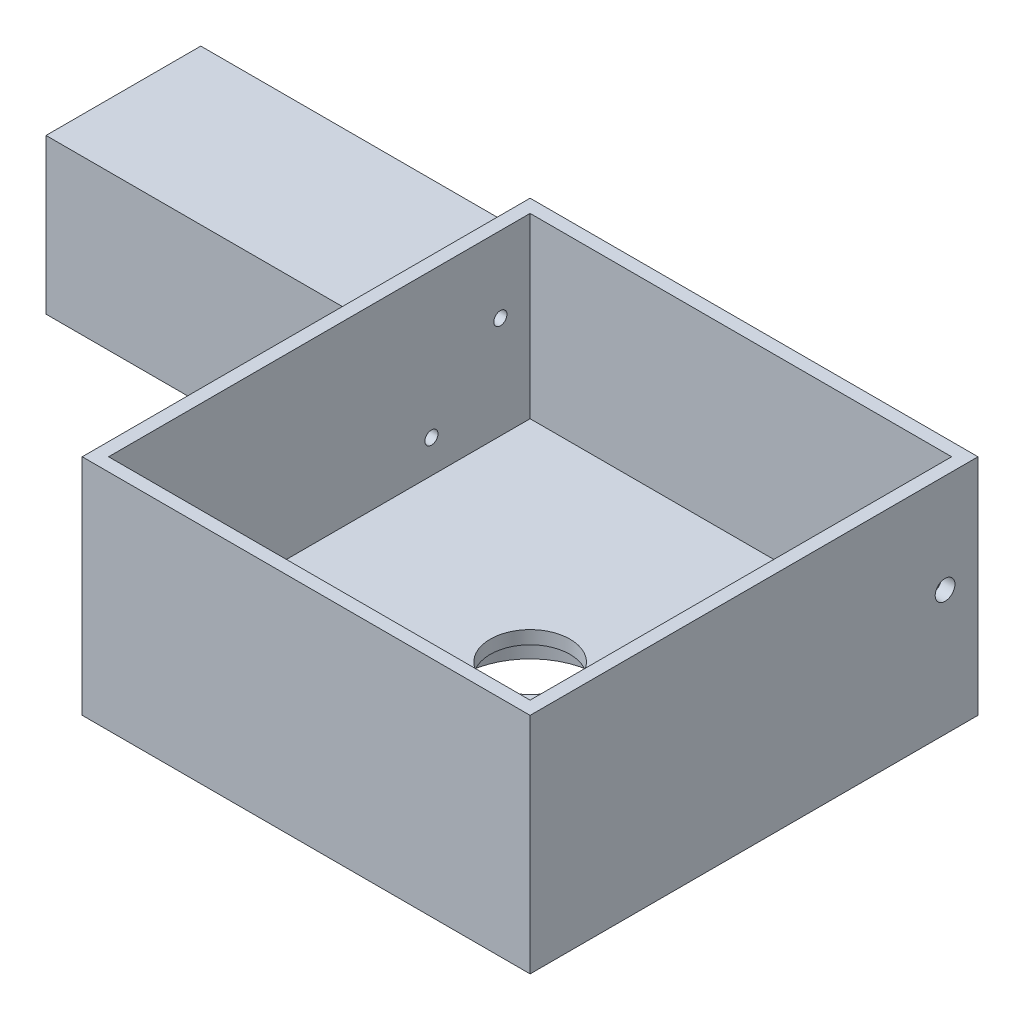
SolidWorks part; units mm, degrees
ref_plane "Front Plane" through (0, 0, 0) normal (0, 0, 1) x (1, 0, 0)
ref_plane "Top Plane" through (0, 0, 0) normal (0, 1, 0) x (1, 0, 0)
ref_plane "Right Plane" through (0, 0, 0) normal (1, 0, 0) x (0, 0, -1)
sketch "Sketch1" plane through (0, 0, 0) normal (0, 1, 0) x (1, 0, 0)
  line L1 (-34, -34) -> (34, -34)
  line L2 (-34, -34) -> (-34, 34)
  line L3 (-34, 34) -> (34, 34)
  line L4 (34, -34) -> (34, 34)
  line L5 (-34, -34) -> (34, 34) construction
  line L6 (-34, 34) -> (34, -34) construction
  point P0 (0, 0)
  dimension "D1" = 68
extrude "Boss-Extrude1" add sketch "Sketch1" along normal blind 34
sketch "Sketch2" plane through (0, 0, 0) normal (0, 1, 0) x (1, 0, 0)
  line L1 (-32, -32) -> (32, -32)
  line L2 (-32, -32) -> (-32, 32)
  line L3 (-32, 32) -> (32, 32)
  line L4 (32, -32) -> (32, 32)
  line L5 (-32, -32) -> (32, 32) construction
  line L6 (-32, 32) -> (32, -32) construction
  point P0 (0, 0)
  dimension "D1" = 64
extrude "Cut-Extrude1" cut sketch "Sketch2" against normal blind 27 from surface at 34 starting at face at (0, 34, 0)
sketch "Sketch5" plane through (0, 0, 0) normal (0, 1, 0) x (1, 0, 0)
  circle A0 centre (0, 0) radius 6.05
  dimension "D1" = 12.1
sketch "Sketch6" plane through (0, 0, 0) normal (0, -1, 0) x (1, 0, 0)
  circle A0 centre (0, 0) radius 10.5
  dimension "D1" = 21
extrude "Cut-Extrude10" cut sketch "Sketch6" against normal blind 5 from surface at 0 starting at face at (0, 0, 0)
sketch "Sketch7" plane through (0, 0, 0) normal (0, -1, 0) x (-1, 0, 0)
  line L0 (-34, 34) -> (34, -34) construction
  line L1 (-34, -34) -> (34, 34) construction
  line L3 (-15, 15) -> (15, 15)
  line L4 (-15, 15) -> (-15, -15)
  line L5 (-15, -15) -> (15, -15)
  line L6 (15, 15) -> (15, -15)
  line L7 (-13, 13) -> (13, 13)
  line L8 (-13, 13) -> (-13, -13)
  line L9 (-13, -13) -> (13, -13)
  line L10 (13, 13) -> (13, -13)
  point P8 (0, 0)
  dimension "D1" = 30
  dimension "D2" = 26
extrude "Cut-Extrude11" cut sketch "Sketch7" against normal blind 2
sketch "Sketch8" plane through (32, 0, 0) normal (-1, 0, 0) x (0, 0, 1)
  line L0 (32, 7) -> (-32, 7) construction
  line L1 (-32, 7) -> (-32, 34) construction
  circle A0 centre (-29, 19) radius 1.5
  dimension "D1" = 3
  dimension "D2" = 12
  dimension "D3" = 3
extrude "Cut-Extrude12" cut sketch "Sketch8" against normal through all
sketch "Sketch9" plane through (-34, 0, 0) normal (-1, 0, 0) x (0, 0, 1)
  line L0 (-34, 29) -> (-10.5, 5.5) construction
  line L1 (-34, 5.5) -> (-10.5, 5.5)
  line L2 (-34, 5.5) -> (-34, 29)
  line L3 (-34, 29) -> (-10.5, 29)
  line L4 (-10.5, 5.5) -> (-10.5, 29)
  line L5 (-10.5, 29) -> (-34, 5.5) construction
  line L6 (-34, 34) -> (-34, 0) construction
  line L7 (-34, 0) -> (34, 0) construction
  circle A0 centre (-22.25, 17.25) radius 5.6
  dimension "D2" = 11.2
  dimension "D3" = 5.5
  dimension "D1" = 23.5
extrude "Boss-Extrude4" add sketch "Sketch9" along normal blind 50
sketch "Sketch11" plane through (-84, 0, 0) normal (-1, 0, 0) x (0, 0, 1)
  line L0 (-34, 29) -> (-10.5, 5.5) construction
  line L2 (-34, 5.5) -> (-10.5, 29) construction
  line L3 (-34, 29) -> (-34, 5.5) construction
  circle A2 centre (-27.4826, 22.4826) radius 1
  circle A3 centre (-17.0174, 12.0174) radius 1
  dimension "D1" = 2
  dimension "D2" = 14.8
extrude "Cut-Extrude13" cut sketch "Sketch11" against normal blind 52
extrude "Cut-Extrude14" cut sketch "Sketch5" along normal through all
fillet "Fillet1" radius 0.5 8 edges at (0, 0, 13) (13, 0, 0) (0, 0, -13) (-13, 0, 0) (0, 0, 15) (15, 0, 0) (0, 0, -15) (-15, 0, 0)
